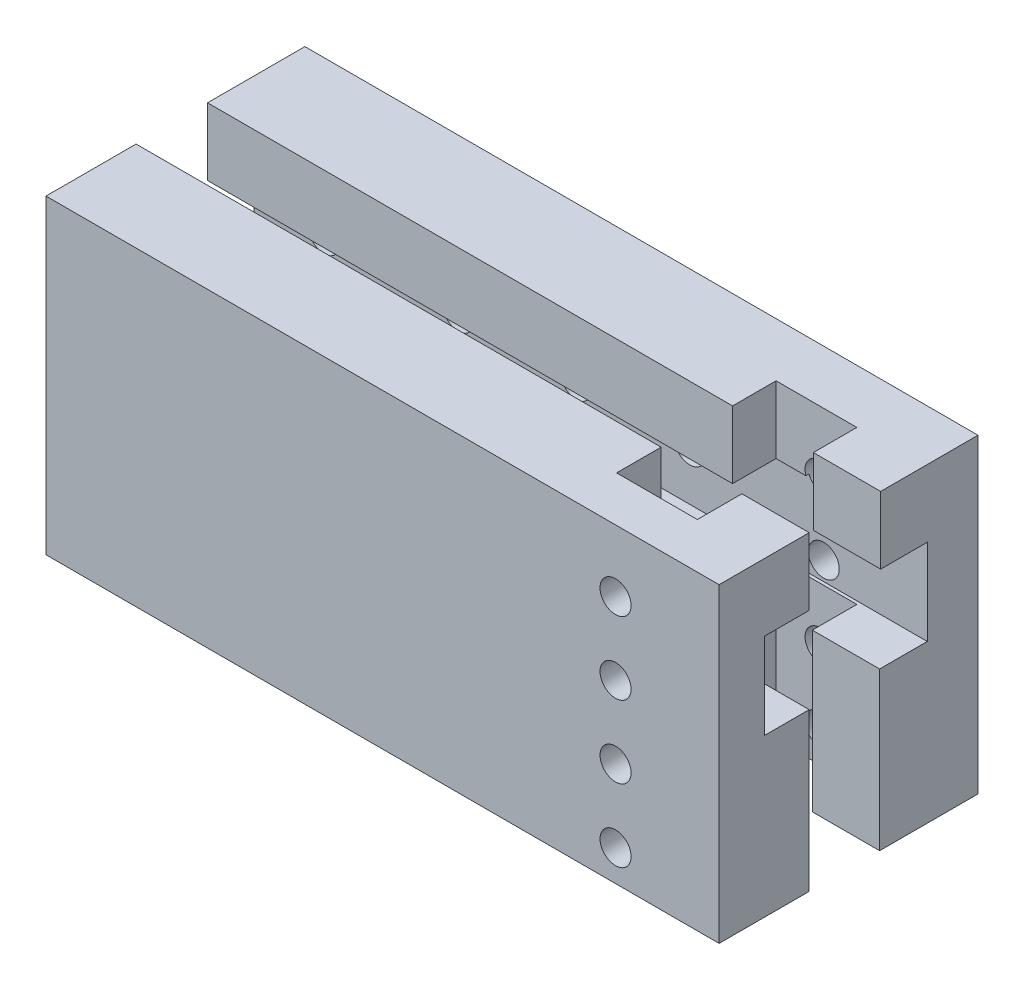
SolidWorks part; units mm, degrees
ref_plane "Front Plane" through (0, 0, 0) normal (0, 0, 1) x (1, 0, 0)
ref_plane "Top Plane" through (0, 0, 0) normal (0, 1, 0) x (1, 0, 0)
ref_plane "Right Plane" through (0, 0, 0) normal (1, 0, 0) x (0, 0, -1)
sketch "Sketch1" plane through (0, 0, 0) normal (0, 0, 1) x (1, 0, 0)
  line L1 (-4.2336, 3.3942) -> (60.7664, 3.3942)
  line L2 (-4.2336, 3.3942) -> (-4.2336, -26.6058)
  line L3 (-4.2336, -26.6058) -> (60.7664, -26.6058)
  line L4 (60.7664, 3.3942) -> (60.7664, -26.6058)
  dimension "D1" = 30
  dimension "D2" = 65
extrude "Boss-Extrude1" add sketch "Sketch1" along normal blind 25
sketch "Sketch2" plane through (0, 3.3942, 0) normal (0, 1, 0) x (1, 0, 0)
  line L0 (60.7664, -25) -> (60.7664, 0) construction
  line L1 (60.7664, -16.3) -> (54.2664, -16.3)
  line L2 (60.7664, -16.3) -> (60.7664, -9.5)
  line L3 (60.7664, -9.5) -> (54.2664, -9.5)
  line L4 (54.2664, -16.3) -> (54.2664, -9.5)
  line L5 (46.4664, -20.6) -> (54.2664, -20.6)
  line L6 (46.4664, -20.6) -> (46.4664, -5.2)
  line L7 (46.4664, -5.2) -> (54.2664, -5.2)
  line L8 (54.2664, -20.6) -> (54.2664, -5.2)
  line L10 (60.7664, -25) -> (-4.2336, -25) construction
  line M4 (60.7664, -25) -> (60.7664, 0)
  dimension "D1" = 0
  dimension "D2" = 0
  dimension "D3" = 4.3
  dimension "D4" = 4.3
  dimension "D5" = 6.8
  dimension "D6" = 8.7
  dimension "D7" = 7.8
  dimension "D8" = 6.5
extrude "Cut-Extrude1" cut sketch "Sketch2" against normal through all contours L4 L1 L3 M4 | L5 L8 L4 L7 L6
sketch "Sketch5" plane through (0, 0, 25) normal (0, 0, 1) x (1, 0, 0)
  line L0 (60.7664, 3.3942) -> (-4.2336, 3.3942) construction
  line L2 (60.7664, -26.6058) -> (60.7664, 3.3942) construction
  circle A0 centre (50.7664, -2.6058) radius 1.5
  circle A1 centre (50.7664, -9.6058) radius 1.5
  circle A2 centre (50.7664, -16.6058) radius 1.5
  circle A3 centre (50.7664, -23.6058) radius 1.5
  dimension "D1" = 3
  dimension "D2" = 6
  dimension "D3" = 3
  dimension "D4" = 10
  dimension "D5" = 3
  dimension "D6" = 7
  dimension "D7" = 10
  dimension "D8" = 3
  dimension "D9" = 7
  dimension "D10" = 7
extrude "Cut-Extrude3" cut sketch "Sketch5" against normal through all
sketch "Sketch6" plane through (-4.2336, 0, 0) normal (-1, 0, 0) x (0, 0, 1)
  line L0 (25, 3.3942) -> (0, 3.3942) construction
  line L1 (9.4, -3.1058) -> (16.3, -3.1058)
  line L2 (9.4, -3.1058) -> (9.4, 3.3942)
  line L3 (9.4, 3.3942) -> (16.3, 3.3942)
  line L4 (16.3, -3.1058) -> (16.3, 3.3942)
  line L5 (4.9, -11.4058) -> (20.6, -11.4058)
  line L6 (4.9, -11.4058) -> (4.9, -3.1058)
  line L7 (4.9, -3.1058) -> (20.6, -3.1058)
  line L8 (20.6, -11.4058) -> (20.6, -3.1058)
  line L9 (25, 3.3942) -> (25, -26.6058) construction
  line M4 (25, 3.3942) -> (0, 3.3942)
  dimension "D1" = 0
  dimension "D2" = 0
  dimension "D3" = 6.9
  dimension "D4" = 4.3
  dimension "D5" = 6.5
  dimension "D6" = 8.7
  dimension "D7" = 4.5
  dimension "D8" = 8.3
extrude "Cut-Extrude4" cut sketch "Sketch6" against normal through all contours L5 L8 L7 L1 L6 | L1 L4 L2 M4
sketch "Sketch7" plane through (0, 0, 0) normal (0, 0, -1) x (-1, 0, 0)
  line L1 (-60.7664, 3.3942) -> (4.2336, 3.3942) construction
  circle A0 centre (-2.5066, -6.6058) radius 1.5
  circle A1 centre (-15.4668, -6.6058) radius 1.5
  circle A2 centre (-26.8531, -6.6058) radius 1.5
  circle A3 centre (-37.8366, -6.6058) radius 1.5
  dimension "D1" = 3
  dimension "D2" = 10
  dimension "D3" = 3
  dimension "D4" = 10
  dimension "D5" = 10
  dimension "D6" = 3
  dimension "D7" = 10
  dimension "D8" = 3
extrude "Cut-Extrude5" cut sketch "Sketch7" against normal blind 10
